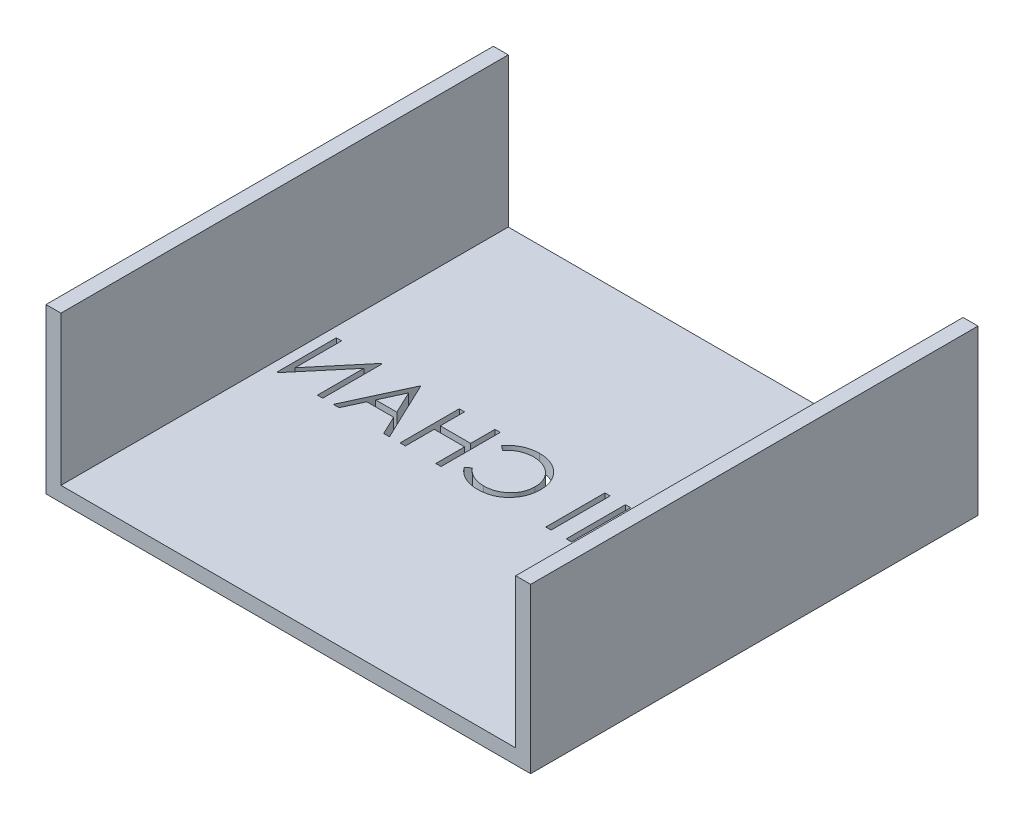
SolidWorks part; units mm, degrees
ref_plane "Front Plane" through (0, 0, 0) normal (0, 0, 1) x (1, 0, 0)
ref_plane "Top Plane" through (0, 0, 0) normal (0, 1, 0) x (1, 0, 0)
ref_plane "Right Plane" through (0, 0, 0) normal (1, 0, 0) x (0, 0, -1)
sketch "Sketch1" plane through (0, 0, 0) normal (0, 1, 0) x (1, 0, 0)
  line L1 (-32.5, 30) -> (32.5, 30)
  line L2 (-32.5, 30) -> (-32.5, -30)
  line L3 (-32.5, -30) -> (32.5, -30)
  line L4 (32.5, 30) -> (32.5, -30)
  line L5 (-32.5, 30) -> (32.5, -30) construction
  line L6 (-32.5, -30) -> (32.5, 30) construction
  point P0 (0, 0)
  dimension "D1" = 65
  dimension "D2" = 60
extrude "Boss-Extrude1" add sketch "Sketch1" along normal blind 2
sketch "Sketch3" plane through (0, 2, 0) normal (0, 1, 0) x (1, 0, 0)
  line L0 (-32.5, 30) -> (-30.5, 30)
  line L1 (-30.5, 30) -> (-30.5, -30)
  line L2 (-32.5, -30) -> (32.5, -30) construction
  line L3 (-30.5, -30) -> (-32.5, -30)
  line L4 (-32.5, -30) -> (-32.5, 30)
  line L6 (32.5, 30) -> (30.5, 30)
  line L7 (32.5, 30) -> (-32.5, 30) construction
  line L8 (30.5, 30) -> (30.5, -30)
  line L9 (30.5, -30) -> (32.5, -30)
  line L10 (32.5, -30) -> (32.5, 30)
  line L11 (-30.5, 0) -> (30.5, 0)
  line M2 (32.5, -30) -> (32.5, 30)
  line M3 (32.5, 30) -> (-32.5, 30)
  line M4 (-32.5, 30) -> (-32.5, -30)
  line M5 (-32.5, -30) -> (32.5, -30)
  dimension "D1" = 61
extrude "Boss-Extrude2" add sketch "Sketch3" along normal blind 20 contours L1 M3 M4 M5 | L8 M3 M5 M2
sketch "Sketch4" plane through (0, 0, 0) normal (0, -1, 0) x (-1, 0, 0)
  text T0 "ONII CHAN" font "Century Gothic" height in points 30
extrude "Cut-Extrude1" cut sketch "Sketch4" against normal blind 20
